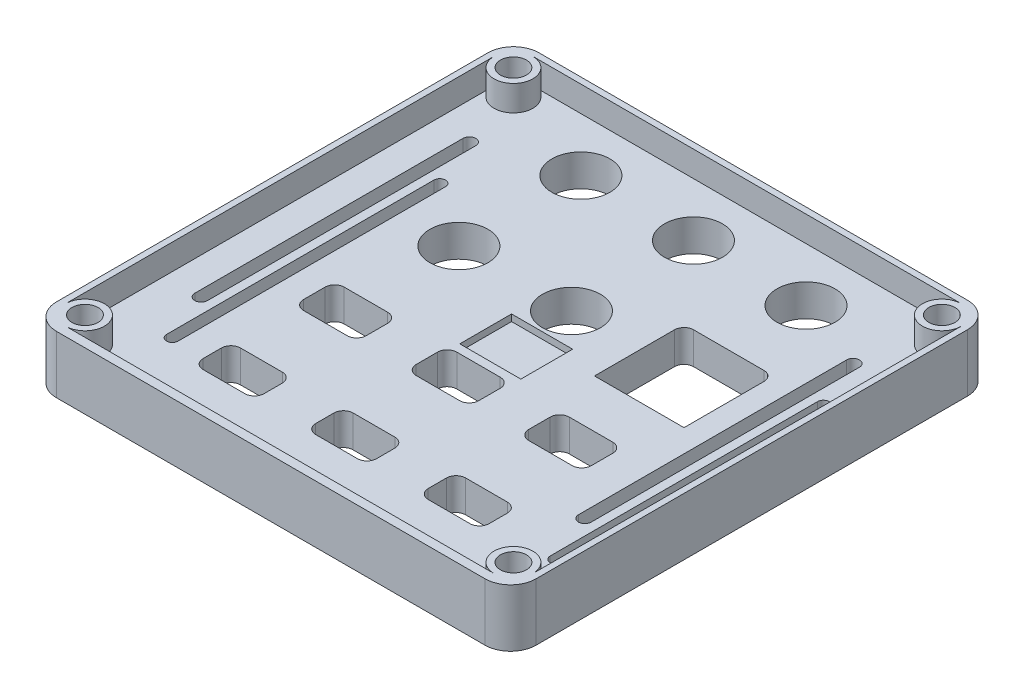
SolidWorks part; units mm, degrees
ref_plane "Front Plane" through (0, 0, 0) normal (0, 0, 1) x (1, 0, 0)
ref_plane "Top Plane" through (0, 0, 0) normal (0, 1, 0) x (1, 0, 0)
ref_plane "Right Plane" through (0, 0, 0) normal (1, 0, 0) x (0, 0, -1)
sketch "Sketch1" plane through (0, 0, 0) normal (0, 1, 0) x (1, 0, 0)
  line L1 (75, -75.45) -> (-75, -75.45)
  line L2 (75, -75.45) -> (75, 75.45)
  line L3 (75, 75.45) -> (-75, 75.45)
  line L4 (-75, -75.45) -> (-75, 75.45)
  line L5 (75, -75.45) -> (-75, 75.45) construction
  line L6 (75, 75.45) -> (-75, -75.45) construction
  point P0 (0, 0)
  dimension "D1" = 150
  dimension "D2" = 150.9
extrude "Boss-Extrude1" add sketch "Sketch1" along normal blind 10 contours L1 L4 L3 L2
sketch "Sketch2" plane through (0, 10, 0) normal (0, 1, 0) x (1, 0, 0)
  line L0 (-75, -75.45) -> (-75, 75.45) construction
  line L1 (75, -75.45) -> (75, 75.45) construction
  line L2 (-35.2, 65.825) -> (-35.2, -36.4502) construction
  line L3 (9.8, -10.475) -> (-9.8, -10.475)
  line L4 (-25.4, -23.175) -> (-45, -23.175)
  line L5 (-25.4, -23.175) -> (-25.4, -10.475)
  line L6 (-25.4, -10.475) -> (-45, -10.475)
  line L7 (-45, -23.175) -> (-45, -10.475)
  line L8 (-25.4, -23.175) -> (-45, -10.475) construction
  line L9 (-25.4, -10.475) -> (-45, -23.175) construction
  line L10 (9.8, -23.175) -> (9.8, -10.475)
  line L11 (9.8, -23.175) -> (-9.8, -23.175)
  line L12 (-9.8, -23.175) -> (-9.8, -10.475)
  line L13 (45, -10.475) -> (25.4, -10.475)
  line L14 (45, -23.175) -> (45, -10.475)
  line L15 (45, -23.175) -> (25.4, -23.175)
  line L16 (25.4, -23.175) -> (25.4, -10.475)
  line L17 (-9.8, -23.175) -> (9.8, -10.475) construction
  line L18 (-9.8, -10.475) -> (9.8, -23.175) construction
  line L19 (25.4, -10.475) -> (45, -23.175) construction
  line L20 (45, -10.475) -> (25.4, -23.175) construction
  line L21 (75, -75.45) -> (-75, -75.45) construction
  line L22 (-25.675, -54.875) -> (-44.725, -54.875)
  line L23 (-25.675, -54.875) -> (-25.675, -43.175)
  line L24 (-25.675, -43.175) -> (-44.725, -43.175)
  line L25 (-44.725, -54.875) -> (-44.725, -43.175)
  line L26 (-25.675, -54.875) -> (-44.725, -43.175) construction
  line L27 (-25.675, -43.175) -> (-44.725, -54.875) construction
  line L28 (75, 75.45) -> (-75, 75.45) construction
  line L29 (9.525, -54.875) -> (9.525, -43.175)
  line L30 (9.525, -43.175) -> (-9.525, -43.175)
  line L31 (9.525, -54.875) -> (-9.525, -54.875)
  line L32 (-9.525, -54.875) -> (-9.525, -43.175)
  line L33 (44.725, -54.875) -> (44.725, -43.175)
  line L34 (44.725, -43.175) -> (25.675, -43.175)
  line L35 (44.725, -54.875) -> (25.675, -54.875)
  line L36 (25.675, -54.875) -> (25.675, -43.175)
  line L37 (25.675, -43.175) -> (44.725, -54.875) construction
  line L38 (44.725, -43.175) -> (25.675, -54.875) construction
  line L39 (35.2, 65.825) -> (35.2, -54.875) construction
  line L40 (0, 18.6) -> (90.9081, 18.6) construction
  line L41 (49.2, 4.6) -> (21.2, 4.6)
  line L42 (49.2, 4.6) -> (49.2, 32.6)
  line L43 (49.2, 32.6) -> (21.2, 32.6)
  line L44 (21.2, 4.6) -> (21.2, 32.6)
  line L45 (49.2, 4.6) -> (21.2, 32.6) construction
  line L46 (49.2, 32.6) -> (21.2, 4.6) construction
  circle A0 centre (-35.2, 56.75) radius 9.075
  circle A1 centre (0, 56.75) radius 9.075
  circle A2 centre (35.2, 56.75) radius 9.075
  circle A3 centre (-35.2, 18.6) radius 9.075
  circle A4 centre (0, 18.6) radius 9.075
  arc A6 (35.2, 9.525) -> (35.2, 27.675) centre (35.2, 18.6) ccw [skipped]
  point P12 (-35.2, -16.825)
  point P17 (-35.2, 47.675)
  point P18 (35.2, -16.825)
  point P20 (0, -16.825)
  point P28 (-35.2, -49.025)
  point P33 (0, 47.675)
  point P34 (-35.2, 65.825)
  point P37 (35.2, -49.025)
  point P48 (-9.075, 56.75)
  point P51 (-26.125, 56.75)
  point P52 (-35.2, 9.525)
  point P55 (35.2, 18.6)
  point P56 (35.2, 18.6)
  point P57 (-35.2, 27.675)
  point P67 (9.075, 18.6)
  dimension "D1" = 18.15
  dimension "D5" = 30
  dimension "D6" = 12.7
  dimension "D7" = 20
  dimension "D16" = 3
  dimension "D11" = 18.15
  dimension "D20" = 20.575
  dimension "D2" = 17.05
  dimension "D3" = 16.15
  dimension "D8" = 19.6
  dimension "D9" = 30
  dimension "D12" = 11.7
  dimension "D13" = 19.05
  dimension "D14" = 70.85
  dimension "D15" = 20
  dimension "D17" = 3
  dimension "D18" = 9.625
  dimension "D19" = 20
  dimension "D21" = 28
  dimension "D22" = 28
  dimension "D23" = 35.2
  dimension "D24" = 35.2
  dimension "D4" = 3
  dimension "D10" = 3
extrude "Cut-Extrude1" cut sketch "Sketch2" against normal up to surface (10 mm away) up to face at (0, 0, 0)
fillet "Fillet1" radius 8 4 edges at (75, 5, -75.45) (75, 5, 75.45) (-75, 5, 75.45) (-75, 5, -75.45)
fillet "Fillet2" radius 3 24 edges at (44.725, 5, 54.875) (44.725, 5, 43.175) (25.675, 5, 54.875) (25.675, 5, 43.175) (9.525, 5, 54.875) (-9.525, 5, 54.875) (9.525, 5, 43.175) (-9.525, 5, 43.175) (-25.675, 5, 54.875) (-44.725, 5, 54.875) (-25.675, 5, 43.175) (-44.725, 5, 43.175) (45, 5, 23.175) (45, 5, 10.475) (25.4, 5, 23.175) (25.4, 5, 10.475) (9.8, 5, 23.175) (9.8, 5, 10.475) (-9.8, 5, 23.175) (-9.8, 5, 10.475) (-25.4, 5, 23.175) (-25.4, 5, 10.475) (-45, 5, 23.175) (-45, 5, 10.475)
sketch "Sketch5" plane through (0, 10, 0) normal (0, 1, 0) x (1, 0, 0)
  line L0 (67, 75.45) -> (-67, 75.45) construction
  line L1 (-75, -67.45) -> (-75, 67.45) construction
  circle A0 centre (-67, 67.45) radius 4.075
  dimension "D1" = 8.15
  dimension "D3" = 8
  dimension "D2" = 8
extrude "Cut-Extrude4" cut sketch "Sketch5" against normal up to surface (10 mm away) up to face at (35.2, 0, 16.825)
mirror "Mirror1" about plane through (0, 0, 0) normal (0, 0, 1) of "Cut-Extrude4"
mirror "Mirror3" about plane through (0, 0, 0) normal (1, 0, 0) of "Cut-Extrude4", "Mirror1"
fillet "Fillet6" radius 3 2 edges at (49.2, 5, -32.6) (21.2, 5, -32.6)
sketch "Sketch7" plane through (0, 10, 0) normal (0, 1, 0) x (1, 0, 0)
  line L0 (58.2784, 48.3846) -> (58.2784, -35.4992) construction
  line L1 (60.2725, 48.3846) -> (60.2725, -35.4992)
  line L2 (56.2843, 48.3846) -> (56.2843, -35.4992)
  line L4 (66.6517, 32.5513) -> (66.6517, -51.0768)
  line L5 (63.0283, 32.5513) -> (63.0283, -51.0768)
  arc A2 (60.2725, 48.3846) -> (56.2843, 48.3846) centre (58.2784, 48.3846) ccw
  arc A3 (56.2843, -35.4992) -> (60.2725, -35.4992) centre (58.2784, -35.4992) ccw
  arc A4 (66.6517, 32.5513) -> (63.0283, 32.5513) centre (64.84, 32.5513) ccw
  arc A5 (63.0283, -51.0768) -> (66.6517, -51.0768) centre (64.84, -51.0768) ccw
  point P6 (58.2784, 6.4427)
  point P12 (64.84, -9.2627)
extrude "Cut-Extrude6" cut sketch "Sketch7" against normal through all
pattern_linear "LPattern3" count 2 spacing 120 along (-1, 0, 0) of "Cut-Extrude6"
sketch "Sketch9" plane through (0, 10, 0) normal (0, 1, 0) x (1, 0, 0)
  circle A0 centre (-67, 67.45) radius 6.075
  circle A1 centre (-67, 67.45) radius 4.075
  dimension "D1" = 2
extrude "Boss-Extrude2" add sketch "Sketch9" along normal blind 8
pattern_linear "LPattern4" count 2 spacing 134 along (1, 0, 0) of "Boss-Extrude2"
pattern_linear "LPattern5" count 2 spacing 134 along (0, 0, 1) of "LPattern4", "Boss-Extrude2"
sketch "Sketch10" plane through (0, 10, 0) normal (0, 1, 0) x (1, 0, 0)
  line L0 (-67, 75.45) -> (67, 75.45)
  line L2 (75, 67.45) -> (75, -67.45)
  line L4 (67, -75.45) -> (-67, -75.45)
  line L6 (-75, -67.45) -> (-75, 67.45)
  line L7 (-75, -67.45) -> (-75, 67.45) construction
  line L9 (-67, 73.525) -> (67, 73.525)
  line L11 (73.075, 67.45) -> (73.075, -66.55)
  line L13 (67, -72.625) -> (-67, -72.625)
  line L15 (-73.075, -66.55) -> (-73.075, 67.45)
  arc A0 (-67, 75.45) -> (-75, 67.45) centre (-67, 67.45) ccw construction
  arc A1 (-75, 67.45) -> (-67, 75.45) centre (-67, 67.45) cw
  arc A2 (67, 75.45) -> (75, 67.45) centre (67, 67.45) cw
  arc A3 (75, -67.45) -> (67, -75.45) centre (67, -67.45) cw
  arc A4 (-67, -75.45) -> (-75, -67.45) centre (-67, -67.45) cw
  circle A5 centre (-67, 67.45) radius 6.075 construction
  circle A6 centre (67, 67.45) radius 6.075 construction
  circle A7 centre (67, 67.45) radius 6.075 construction
  circle A8 centre (67, -66.55) radius 6.075 construction
  circle A9 centre (67, -66.55) radius 6.075 construction
  circle A10 centre (-67, -66.55) radius 6.075 construction
  circle A11 centre (-67, -66.55) radius 6.075 construction
  circle A12 centre (-67, 67.45) radius 6.075 construction
  arc A13 (-73.075, 67.45) -> (-67, 73.525) centre (-67, 67.45) cw
  arc A14 (67, 73.525) -> (73.075, 67.45) centre (67, 67.45) cw
  arc A15 (67, -72.625) -> (73.075, -66.55) centre (67, -66.55) ccw
  arc A16 (-67, -72.625) -> (-73.075, -66.55) centre (-67, -66.55) cw
extrude "Boss-Extrude4" add sketch "Sketch10" along normal blind 8
sketch "Sketch12" plane through (0, 10, 0) normal (0, 1, 0) x (1, 0, 0)
  line L1 (-8.5637, 8.429) -> (10.5363, 8.429)
  line L2 (-8.5637, 8.429) -> (-8.5637, -7.771)
  line L3 (-8.5637, -7.771) -> (10.5363, -7.771)
  line L4 (10.5363, 8.429) -> (10.5363, -7.771)
  dimension "D1" = 19.1
  dimension "D2" = 16.2
extrude "Cut-Extrude7" cut sketch "Sketch12" against normal blind 2.07
